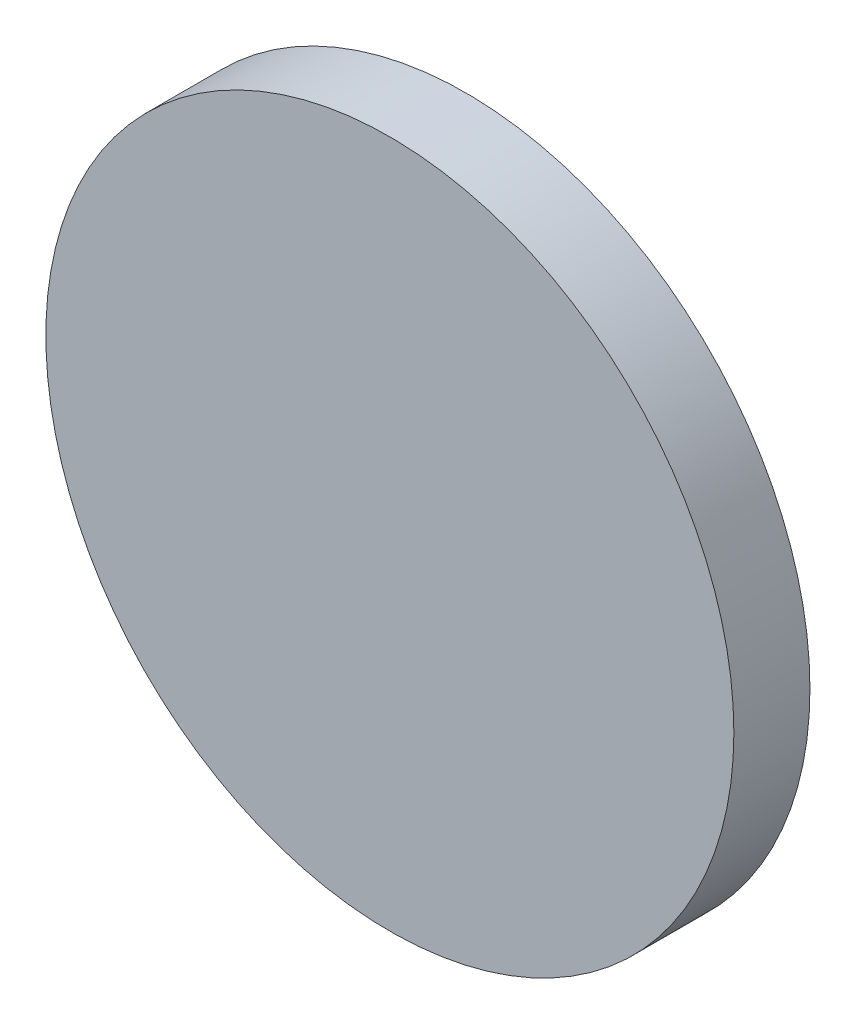
SolidWorks part; units mm, degrees
ref_plane "前视基准面" through (0, 0, 0) normal (0, 0, 1) x (1, 0, 0)
ref_plane "上视基准面" through (0, 0, 0) normal (0, 1, 0) x (1, 0, 0)
ref_plane "右视基准面" through (0, 0, 0) normal (1, 0, 0) x (0, 0, -1)
sketch "草图1" plane through (0, 0, 0) normal (1, 0, 0) x (0, 0, -1)
  line L0 (0, 0) -> (41.7729, 0) construction
  line L1 (0, 10.4) -> (2.3, 10.4)
  line L2 (2.3, 10.4) -> (2.3, 4.4)
  line L3 (2.3, 4.4) -> (5.5, 4.4)
  line L4 (5.5, 4.4) -> (5.5, 0)
  line L5 (0, 10.4) -> (0, 0)
  line L6 (0, 0) -> (5.5, 0)
  dimension "D1" = 8.8
  dimension "D2" = 5.5
  dimension "D3" = 2.3
  dimension "D4" = 20.8
revolve "旋转1" add sketch "草图1" angle 360 about L0
sketch "草图2" plane through (0, 0, -5.5) normal (0, 0, -1) x (-1, 0, 0)
  circle A0 centre (0, 0) radius 2.6
  dimension "D1" = 5.2
extrude "切除-拉伸1" cut sketch "草图2" against normal blind 3
